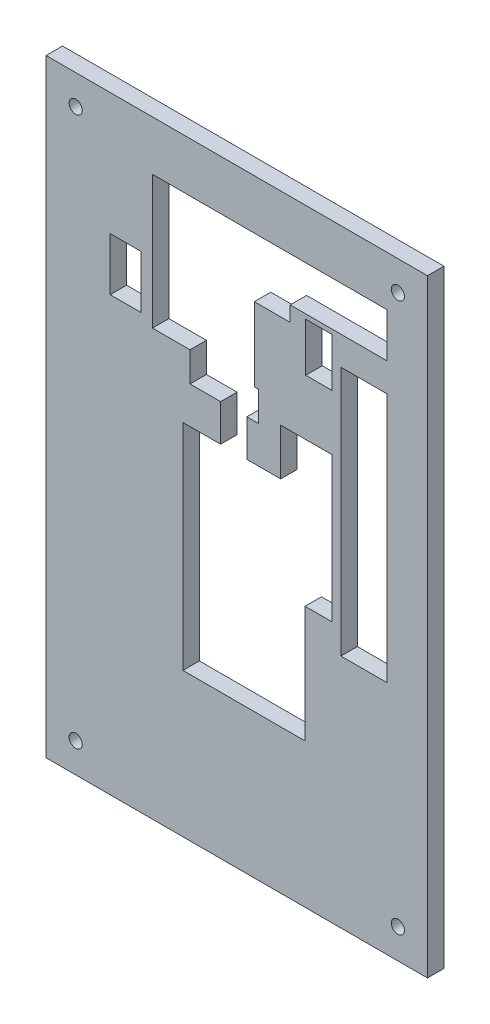
SolidWorks part; units mm, degrees
ref_plane "Front Plane" through (0, 0, 0) normal (0, 0, 1) x (1, 0, 0)
ref_plane "Top Plane" through (0, 0, 0) normal (0, 1, 0) x (1, 0, 0)
ref_plane "Right Plane" through (0, 0, 0) normal (1, 0, 0) x (0, 0, -1)
sketch "Sketch9" plane through (0, 0, 0) normal (0, 0, 1) x (1, 0, 0)
  line L0 (107.1038, -20.8967) -> (121.1436, -20.8967)
  line L1 (121.1436, -20.8967) -> (121.1436, 55.1711)
  line L2 (121.1436, 55.1711) -> (107.1038, 55.1711)
  line L3 (107.1038, 55.1711) -> (107.1038, -20.8967)
  line L4 (17.4236, -92.5411) -> (133.4236, -92.5411)
  line L5 (133.4236, -92.5411) -> (133.4236, 92.4589)
  line L6 (133.4236, 92.4589) -> (17.4236, 92.4589)
  line L7 (17.4236, 92.4589) -> (17.4236, -92.5411)
  line L8 (96.4008, 47.7167) -> (104.4442, 47.7167)
  line L9 (104.4442, 47.7167) -> (104.4442, 62.4805)
  line L10 (104.4442, 62.4805) -> (96.4008, 62.4805)
  line L11 (96.4008, 62.4805) -> (96.4008, 47.7167)
  line L12 (88.7925, 30.7834) -> (104.4559, 30.7834)
  line L13 (104.4559, 30.7834) -> (104.4559, 16.0196)
  line L14 (104.4559, 16.0196) -> (104.4559, -13.2439)
  line L15 (104.4559, -13.2439) -> (96.1886, -13.2439)
  line L16 (96.1886, -13.2439) -> (96.1886, -28.708)
  line L17 (96.1886, -28.708) -> (96.1886, -48.708)
  line L18 (96.1886, -48.708) -> (59.0411, -48.708)
  line L19 (59.0411, -48.708) -> (59.0411, -28.708)
  line L20 (59.0411, -28.708) -> (59.0411, 16.6008)
  line L21 (59.0411, 16.6008) -> (70.4989, 16.6008)
  line L22 (70.4989, 16.6008) -> (70.4989, 27.8192)
  line L23 (70.4989, 27.8192) -> (61.1857, 27.8192)
  line L24 (61.1857, 27.8192) -> (61.1857, 28.9577)
  line L25 (61.1857, 28.9577) -> (61.1857, 36.8241)
  line L26 (61.1857, 36.8241) -> (49.7696, 36.8241)
  line L27 (49.7696, 36.8241) -> (49.7696, 77.3371)
  line L28 (49.7696, 77.3371) -> (80.7576, 77.3371)
  line L29 (80.7576, 77.3371) -> (91.6664, 77.3371)
  line L30 (91.6664, 77.3371) -> (121.1436, 77.3371)
  line L31 (121.1436, 77.3371) -> (121.1436, 63.8829)
  line L32 (121.1436, 63.8829) -> (91.6664, 63.8829)
  line L33 (91.6664, 63.8829) -> (91.6664, 59.2791)
  line L34 (91.6664, 59.2791) -> (80.7576, 59.2791)
  line L35 (80.7576, 59.2791) -> (80.7576, 36.8241)
  line L36 (80.7576, 36.8241) -> (81.982, 36.8241)
  line L37 (81.982, 36.8241) -> (81.982, 28.9577)
  line L38 (81.982, 28.9577) -> (81.982, 27.8192)
  line L39 (81.982, 27.8192) -> (78.4893, 27.8192)
  line L40 (78.4893, 27.8192) -> (78.4893, 16.6008)
  line L41 (78.4893, 16.6008) -> (88.7925, 16.6008)
  line L42 (88.7925, 16.6008) -> (88.7925, 30.7834)
  line L43 (36.9218, 39.1964) -> (46.288, 39.1964)
  line L44 (46.288, 39.1964) -> (46.288, 55.283)
  line L45 (46.288, 55.283) -> (36.9218, 55.283)
  line L46 (36.9218, 55.283) -> (36.9218, 39.1964)
  ellipse E0 centre (26.4237, 83.4589) end of major axis (28.4238, 83.4589) minor radius 2
  ellipse E1 centre (124.4237, 83.4589) end of major axis (126.4238, 83.4589) minor radius 2
  ellipse E2 centre (124.4237, -83.5411) end of major axis (126.4238, -83.5411) minor radius 2
  ellipse E3 centre (26.4237, -83.5411) end of major axis (28.4238, -83.5411) minor radius 2
extrude "Boss-Extrude3" add sketch "Sketch9" along normal blind 5
